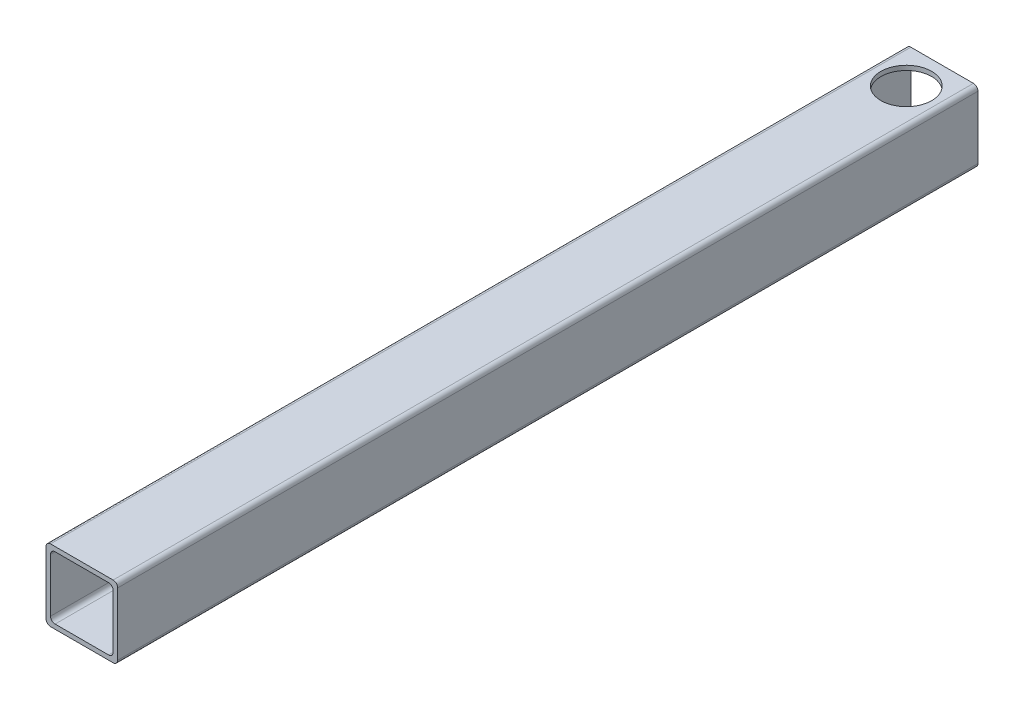
SolidWorks part; units mm, degrees
material "ASTM A36 Steel"
ref_plane "Front Plane" through (0, 0, 0) normal (0, 0, 1) x (1, 0, 0)
ref_plane "Top Plane" through (0, 0, 0) normal (0, 1, 0) x (1, 0, 0)
ref_plane "Right Plane" through (0, 0, 0) normal (1, 0, 0) x (0, 0, -1)
sketch "Sketch1" plane through (0, 0, 0) normal (0, 0, 1) x (1, 0, 0)
  line L0 (-14.224, -16.637) -> (14.224, -16.637)
  line L1 (-16.637, -14.224) -> (-16.637, 14.224)
  line L2 (14.224, 16.637) -> (-14.224, 16.637)
  line L3 (16.637, 14.224) -> (16.637, -14.224)
  line L4 (-16.637, -19.05) -> (16.637, -19.05)
  line L5 (-19.05, -16.637) -> (-19.05, 16.637)
  line L6 (16.637, 19.05) -> (-16.637, 19.05)
  line L7 (19.05, 16.637) -> (19.05, -16.637)
  line L10 (-16.637, 0) -> (16.637, 0) construction
  arc A0 (19.05, 16.637) -> (16.637, 19.05) centre (16.637, 16.637) ccw
  arc A1 (16.637, -19.05) -> (19.05, -16.637) centre (16.637, -16.637) ccw
  arc A2 (-19.05, -16.637) -> (-16.637, -19.05) centre (-16.637, -16.637) ccw
  arc A3 (-16.637, 19.05) -> (-19.05, 16.637) centre (-16.637, 16.637) ccw
  arc A4 (-14.224, 16.637) -> (-16.637, 14.224) centre (-14.224, 14.224) ccw
  arc A5 (16.637, 14.224) -> (14.224, 16.637) centre (14.224, 14.224) ccw
  arc A6 (14.224, -16.637) -> (16.637, -14.224) centre (14.224, -14.224) ccw
  arc A7 (-16.637, -14.224) -> (-14.224, -16.637) centre (-14.224, -14.224) ccw
extrude "Boss-Extrude1" add sketch "Sketch1" along normal blind 457.2
sketch "Sketch2" plane through (0, 0, 0) normal (0, 1, 0) x (1, 0, 0)
  line L0 (0, -20.955) -> (0, 20.955) construction
  line L1 (-20.955, 0) -> (20.955, 0) construction
  circle A0 centre (0, -19.05) radius 13.4938
  dimension "D1" = 26.9875
  dimension "D2" = 19.05
extrude "Cut-Extrude1" cut sketch "Sketch2" against normal mid plane 457.2
